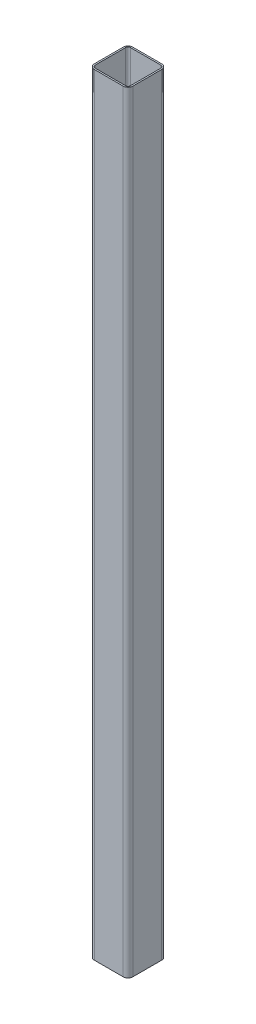
SolidWorks part; units mm, degrees
ref_plane "Front Plane" through (0, 0, 0) normal (0, 0, 1) x (1, 0, 0)
ref_plane "Top Plane" through (0, 0, 0) normal (0, 1, 0) x (1, 0, 0)
ref_plane "Right Plane" through (0, 0, 0) normal (1, 0, 0) x (0, 0, -1)
sketch "Sketch1" plane through (0, 0, 0) normal (0, 1, 0) x (1, 0, 0)
  line L0 (-30.2895, -35.052) -> (30.2895, -35.052)
  line L1 (-35.052, -30.2895) -> (-35.052, 30.2895)
  line L2 (30.2895, 35.052) -> (-30.2895, 35.052)
  line L3 (35.052, 30.2895) -> (35.052, -30.2895)
  line L4 (-28.575, -38.1) -> (28.575, -38.1)
  line L5 (-38.1, -28.575) -> (-38.1, 28.575)
  line L6 (28.575, 38.1) -> (-28.575, 38.1)
  line L7 (38.1, 28.575) -> (38.1, -28.575)
  line L10 (0, 35.052) -> (0, -35.052) construction
  arc A0 (38.1, 28.575) -> (28.575, 38.1) centre (28.575, 28.575) ccw
  arc A1 (28.575, -38.1) -> (38.1, -28.575) centre (28.575, -28.575) ccw
  arc A2 (-38.1, -28.575) -> (-28.575, -38.1) centre (-28.575, -28.575) ccw
  arc A3 (-28.575, 38.1) -> (-38.1, 28.575) centre (-28.575, 28.575) ccw
  arc A4 (-30.2895, 35.052) -> (-35.052, 30.2895) centre (-30.2895, 30.2895) ccw
  arc A5 (35.052, 30.2895) -> (30.2895, 35.052) centre (30.2895, 30.2895) ccw
  arc A6 (30.2895, -35.052) -> (35.052, -30.2895) centre (30.2895, -30.2895) ccw
  arc A7 (-35.052, -30.2895) -> (-30.2895, -35.052) centre (-30.2895, -30.2895) ccw
extrude "Boss-Extrude1" add sketch "Sketch1" along normal mid plane 1524
